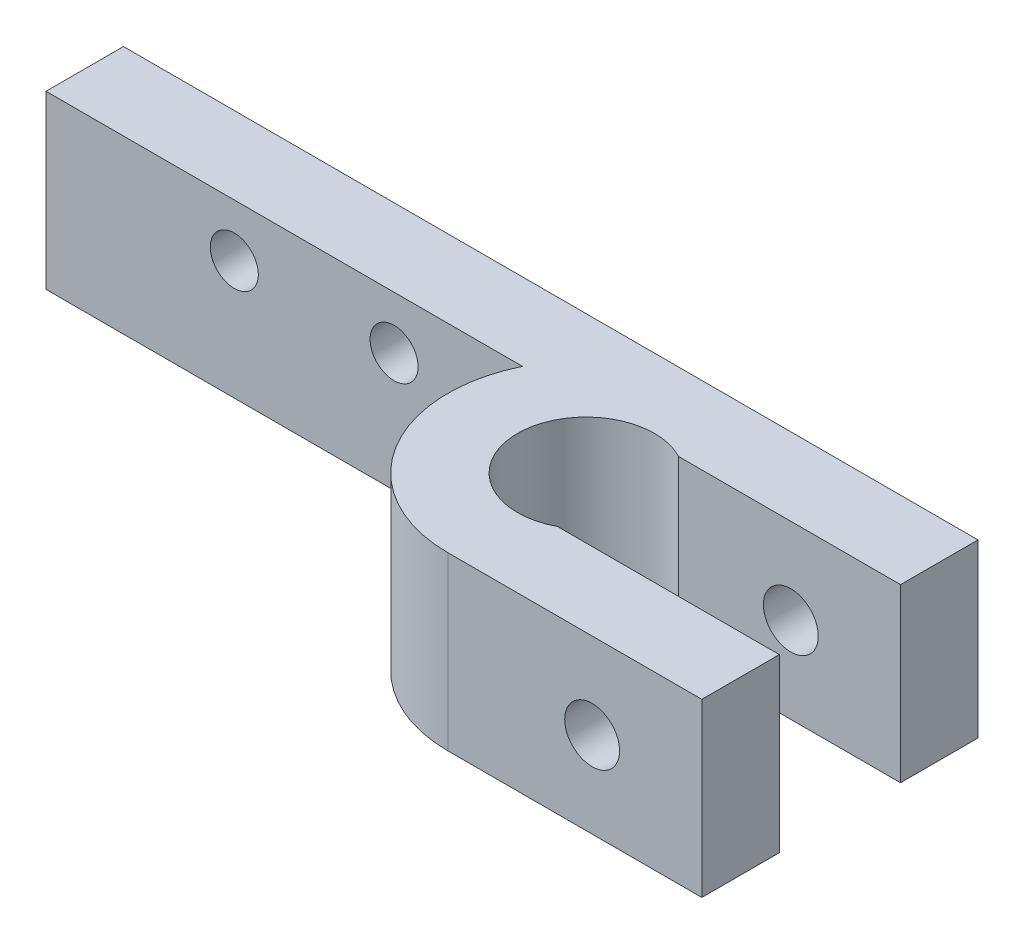
SolidWorks part; units mm, degrees
ref_plane "Front Plane" through (0, 0, 0) normal (0, 0, 1) x (1, 0, 0)
ref_plane "Top Plane" through (0, 0, 0) normal (0, 1, 0) x (1, 0, 0)
ref_plane "Right Plane" through (0, 0, 0) normal (1, 0, 0) x (0, 0, -1)
sketch "Sketch1" plane through (0, 0, 0) normal (0, 1, 0) x (1, 0, 0)
  line L1 (-49.85, 0) -> (0, 0)
  line L2 (0, -11.59) -> (0, -16.11)
  line L3 (-22.87, -8.055) -> (-22.87, -31.8793) construction
  line L4 (0, -4.52) -> (-14.815, -4.52)
  line L5 (-14.815, -11.59) -> (0, -11.59)
  line L6 (-22.0529, -4.52) -> (-49.85, -4.52)
  line L7 (0, 0) -> (0, -4.52)
  line L9 (-14.815, -16.11) -> (0, -16.11)
  line L11 (-49.85, -4.52) -> (-49.85, 0)
  arc A1 (-22.0529, -4.52) -> (-14.815, -16.11) centre (-14.815, -8.055) ccw
  arc A2 (-14.815, -4.52) -> (-14.815, -11.59) centre (-14.815, -8.055) ccw
  dimension "D1" = 49.85
  dimension "D2" = 4.52
  dimension "D3" = 4.52
  dimension "D4" = 16.11
  dimension "D5" = 22.87
extrude "Boss-Extrude1" add sketch "Sketch1" along normal blind 10.01
sketch "Sketch2" plane through (0, 10.01, 0) normal (0, 1, 0) x (1, 0, 0)
  circle A0 centre (-14.815, -8.055) radius 4
  dimension "D1" = 8
extrude "Cut-Extrude1" cut sketch "Sketch2" against normal through all
sketch "Sketch3" plane through (0, 0, 0) normal (0, 0, -1) x (-1, 0, 0)
  line L0 (0, 5.005) -> (4.2, 5.005) construction
  line L2 (0, 10.01) -> (0, 0) construction
  line L3 (4.2, 5.005) -> (4.2, 10.01) construction
  line L4 (0, 10.01) -> (49.85, 10.01) construction
  line L5 (4.2, 5.005) -> (4.2, 0) construction
  line L6 (0, 0) -> (49.85, 0) construction
  circle A0 centre (6.3999, 5.005) radius 1.6
  dimension "D1" = 4.2
  dimension "D2" = 3.2
extrude "Cut-Extrude2" cut sketch "Sketch3" against normal through all
sketch "Sketch5" plane through (0, 0, 0) normal (0, 0, -1) x (-1, 0, 0)
  line L0 (24.925, 0) -> (24.925, 10.01) construction
  line L1 (0, 0) -> (49.85, 0) construction
  line L2 (0, 10.01) -> (49.85, 10.01) construction
  line L4 (38.865, 6.94) -> (29.545, 6.94) construction
  circle A0 centre (29.545, 6.94) radius 1.4
  circle A2 centre (38.865, 6.94) radius 1.4
  dimension "D1" = 2.8
  dimension "D2" = 4.62
  dimension "D4" = 2.8
  dimension "D3" = 9.32
  dimension "D5" = 3.07
extrude "Cut-Extrude3" cut sketch "Sketch5" against normal up to next
